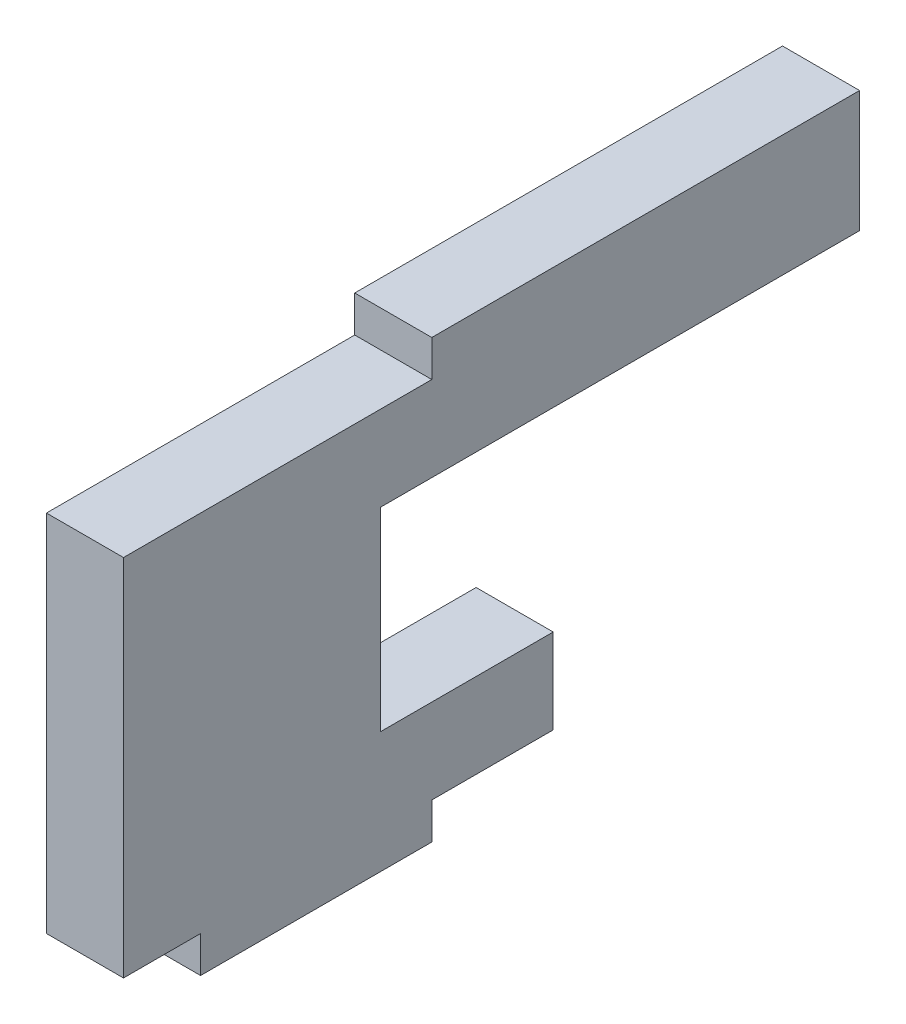
SolidWorks part; units mm, degrees
ref_plane "Front Plane" through (0, 0, 0) normal (0, 0, 1) x (1, 0, 0)
ref_plane "Top Plane" through (0, 0, 0) normal (0, 1, 0) x (1, 0, 0)
ref_plane "Right Plane" through (0, 0, 0) normal (1, 0, 0) x (0, 0, -1)
sketch "Sketch1" plane through (0, 0, 0) normal (1, 0, 0) x (0, -1, 0)
  line L1 (0, 0) -> (16.5, 0)
  line L2 (0, 0) -> (0, 43)
  line L3 (0, 43) -> (16.5, 43)
  line L4 (16.5, 0) -> (16.5, 43)
extrude "Boss-Extrude1" add sketch "Sketch1" along normal blind 3.175
sketch "Sketch2" plane through (3.175, 0, 0) normal (1, 0, 0) x (0, 0, -1)
  line L0 (9.525, 0) -> (9.525, -16.5) construction
  line L1 (55, 0) -> (-55, 0) construction
  line L2 (0, -16.5) -> (43, -16.5) construction
  line L3 (0, 55) -> (0, -55) construction
  line L4 (0, -1.5) -> (9.525, -1.5) construction
  line L6 (0, 0) -> (9.525, 0)
  line L7 (0, 0) -> (0, -1.5)
  line L8 (0, -1.5) -> (9.525, -1.5)
  line L9 (9.525, 0) -> (9.525, -1.5)
  dimension "D1" = 9.525
  dimension "D2" = 15
extrude "Cut-Extrude1" cut sketch "Sketch2" against normal blind 10
sketch "Sketch3" plane through (3.175, 0, 0) normal (1, 0, 0) x (0, 0, -1)
  line L15 (9.525, 104.7435) -> (9.525, 89.7435) construction
  line L16 (14.525, -5) -> (43, -5)
  line L17 (0, 1.7463) -> (0, -1.7463) construction
  line L18 (0, -16.5) -> (43, -16.5) construction
  line L24 (14.525, -16.5) -> (14.525, -5)
  line L27 (14.525, -16.5) -> (43, -16.5)
  line L28 (43, -16.5) -> (43, -5)
  line L29 (1.7463, 0) -> (-1.7463, 0) construction
  dimension "D2" = 5
  dimension "D1" = 9.525
  dimension "D3" = 5
extrude "Cut-Extrude2" cut sketch "Sketch3" against normal through all
sketch "Sketch4" plane through (3.175, 0, 0) normal (1, 0, 0) x (0, 0, -1)
  line L0 (43, -5) -> (14.525, -5) construction
  line L1 (9.525, -1.5) -> (9.525, 0) construction
  circle A0 centre (19.705, -2) radius 1.5
  dimension "D1" = 3
  dimension "D2" = 10.18
extrude "Cut-Extrude3" [suppressed] cut sketch "Sketch4" against normal through all
sketch "Sketch5" plane through (3.175, 0, 0) normal (1, 0, 0) x (0, 0, -1)
  line L0 (0, 1.7463) -> (0, -1.7463) construction
  line L1 (0, -16.5) -> (-3.175, -16.5)
  line L2 (0, -16.5) -> (0, -1.5)
  line L3 (0, -1.5) -> (-3.175, -1.5)
  line L4 (-3.175, -16.5) -> (-3.175, -1.5)
  line L5 (0, -16.5) -> (14.525, -16.5) construction
  line L6 (0, -1.5) -> (9.525, -1.5) construction
  dimension "D1" = 3.175
  dimension "D2" = 0
extrude "Boss-Extrude2" add sketch "Sketch5" against normal up to surface (3.175 mm away) up to face at (0, -5.75, -16.7625)
sketch "Sketch6" plane through (3.175, 0, 0) normal (1, 0, 0) x (0, 0, -1)
  line L0 (1.7463, 0) -> (-1.7463, 0) construction
  line L1 (27.1458, 0) -> (43, 0)
  line L2 (27.1458, 0) -> (27.1458, -5)
  line L3 (27.1458, -5) -> (43, -5)
  line L4 (43, 0) -> (43, -5)
  line L6 (14.525, -5) -> (7.4187, -5)
  line L7 (14.525, -5) -> (14.525, -13.0064)
  line L8 (14.525, -13.0064) -> (7.4187, -13.0064)
  line L9 (7.4187, -5) -> (7.4187, -13.0064)
extrude "Cut-Extrude4" cut sketch "Sketch6" against normal blind 10
sketch "Sketch7" plane through (3.175, 0, 0) normal (1, 0, 0) x (0, 0, -1)
  line L0 (0, 1.7463) -> (0, -1.7463) construction
  line L4 (0, -16.5) -> (0, -18)
  line L5 (0, -18) -> (9.525, -18)
  line L6 (9.525, -18) -> (9.525, -16.5)
  line L7 (-3.175, -16.5) -> (14.525, -16.5) construction
  line L8 (9.525, -16.5) -> (0, -16.5)
  dimension "D1" = 9.525
extrude "Boss-Extrude3" add sketch "Sketch7" against normal up to surface (3.175 mm away) up to face at (0, -7.2013, -11.0879)
